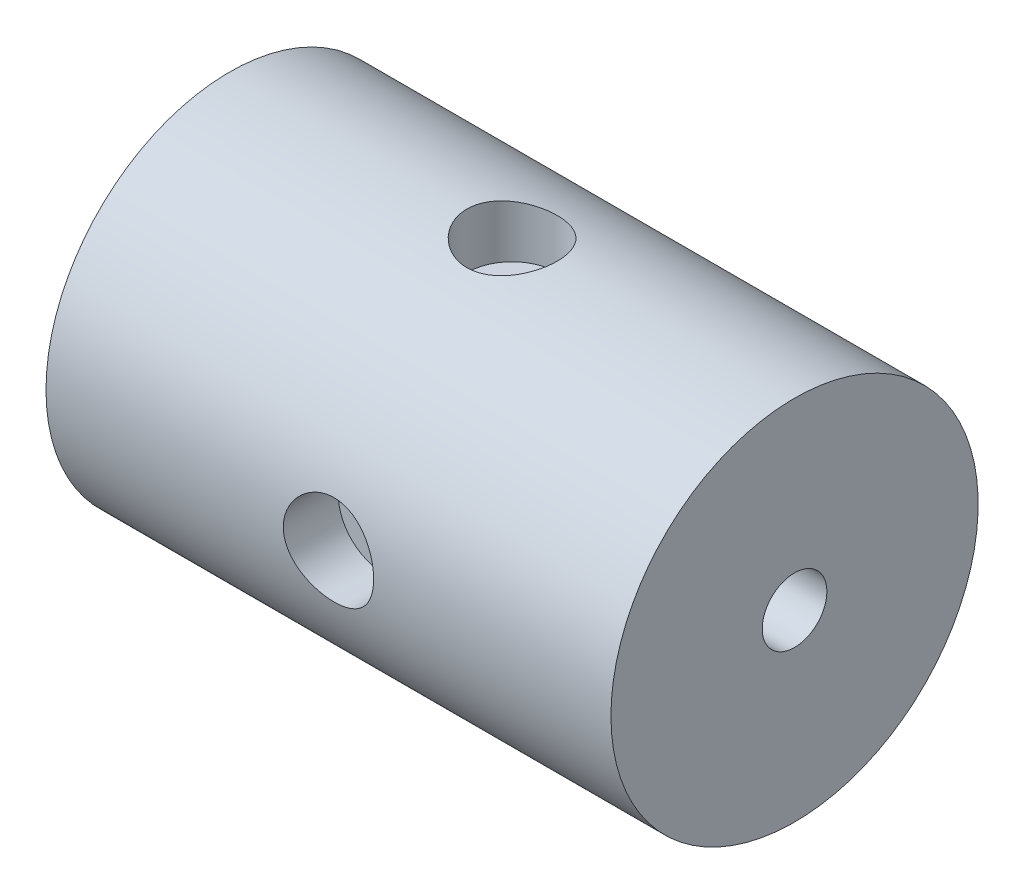
SolidWorks part; units mm, degrees
ref_plane "Ebene vorne" through (0, 0, 0) normal (0, 0, 1) x (1, 0, 0)
ref_plane "Ebene oben" through (0, 0, 0) normal (0, 1, 0) x (1, 0, 0)
ref_plane "Ebene rechts" through (0, 0, 0) normal (1, 0, 0) x (0, 0, -1)
sketch "Skizze1" plane through (0, 0, 0) normal (0, 0, 1) x (1, 0, 0)
  line L0 (0, 0) -> (100, 0) construction
  line L1 (0, 17.25) -> (0, 32.5)
  line L2 (0, 32.5) -> (100, 32.5)
  line L3 (100, 32.5) -> (100, 1.5)
  line L4 (0, 17.25) -> (76.6256, 17.25)
  line L5 (76.6256, 17.25) -> (85, 1.5)
  line L6 (85, 1.5) -> (100, 1.5)
  line L7 (100, 1.5) -> (100, 0) construction
  line L8 (0, 17.25) -> (0, 0) construction
  dimension "D1" = 100
  dimension "D2" = 34.5
  dimension "D3" = 65
  dimension "D4" = 118
  dimension "D5" = 3
  dimension "D6" = 15
revolve "Rotation1" add sketch "Skizze1" angle 360 about L0
sketch "Skizze3" plane through (100, 0, 0) normal (1, 0, 0) x (0, 0, -1)
  point P0 (0, 0)
hole_wizard "G1/4 Gewindebohrung1" positions "3D-Skizze2" profile "Skizze5" tap size "G1/4" standard "DIN" end condition up to next
sketch3d "3D-Skizze2"
  point P0 (100, 0, 0)
sketch "Skizze5" plane through (100, 0, 0) normal (0, 1, 0) x (0, 0, -1)
  line L0 (0, 0) -> (0, 100)
  line L1 (0, 100) -> (5.7225, 100)
  line L2 (5.7225, 100) -> (5.7225, 0)
  line L5 (5.7225, 0) -> (0, 0)
  line L11 (0, -6.35) -> (0, 107.95) construction
  dimension "Bohrerdurchmesser" = 11.445
  dimension "Bohrungstiefe" = 100
cosmetic thread "Bohrungsgewinde1" parameters "D2"=13.157
ref_plane "Ebene1" through (0, 0, 32.5) normal (0, 0, 1) x (1, 0, 0)
sketch "Skizze6" plane through (0, 0, 32.5) normal (0, 0, 1) x (1, 0, 0)
  circle A0 centre (50, 0) radius 8
  point P0 (50, 0)
  dimension "D2" = 16
  dimension "D1" = 50
extrude "Schnitt-Linear austragen1" cut sketch "Skizze6" against normal blind 9.75
sketch "Skizze7" plane through (0, 0, 32.5) normal (0, 0, 1) x (1, 0, 0)
  circle A0 centre (50, 0) radius 5
  dimension "D1" = 10
extrude "Schnitt-Linear austragen2" cut sketch "Skizze7" against normal blind 30
pattern_circular "Kreismuster1" count 3 every 90 about axis through (0, 0, 0) along (1, 0, 0) of "Schnitt-Linear austragen1", "Schnitt-Linear austragen2"
